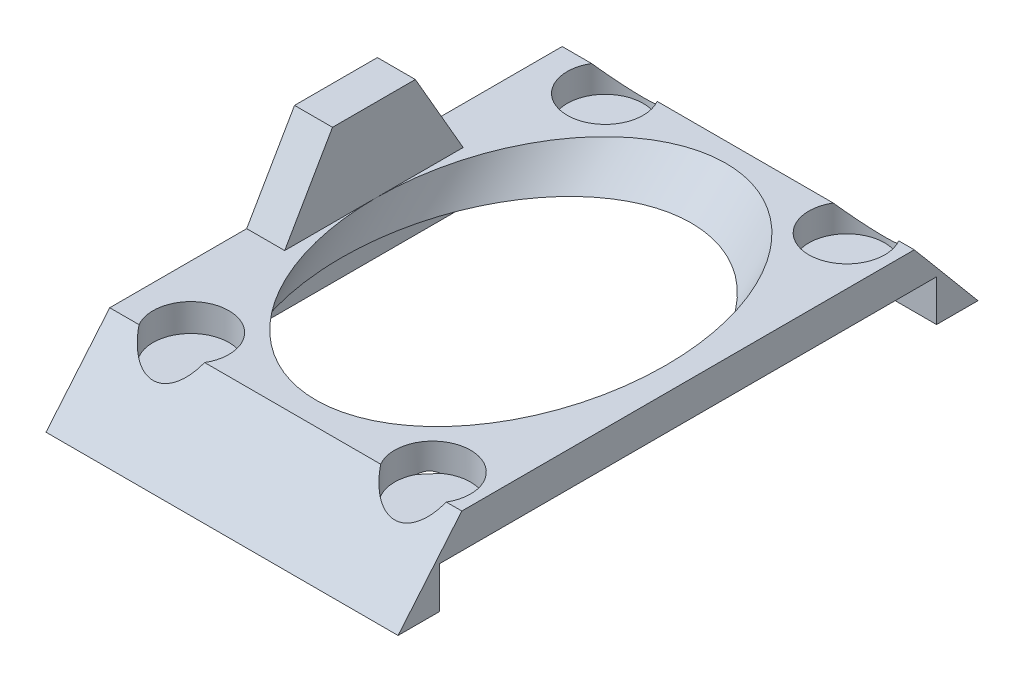
SolidWorks part; units mm, degrees
ref_plane "Front Plane" through (0, 0, 0) normal (0, 0, 1) x (1, 0, 0)
ref_plane "Top Plane" through (0, 0, 0) normal (0, 1, 0) x (1, 0, 0)
ref_plane "Right Plane" through (0, 0, 0) normal (1, 0, 0) x (0, 0, -1)
sketch "Sketch1" plane through (0, 0, 0) normal (0, 1, 0) x (1, 0, 0)
  line L1 (-13, 21) -> (12.5, 21)
  line L2 (-13, 21) -> (-13, -21)
  line L3 (-13, -21) -> (12.5, -21)
  line L4 (12.5, 21) -> (12.5, -21)
  dimension "D1" = 25.5
  dimension "D2" = 42
  dimension "D3" = 21
  dimension "D4" = 12.5
extrude "Boss-Extrude1" add sketch "Sketch1" along normal blind 5.5 contours L1 L4 L3 L2
ref_plane "Plane4" through (-13, 0, 0) normal (-1, 0, 0) x (0, 0, 1)
sketch "Sketch2" plane through (0, 0, 0) normal (0, -1, 0) x (1, 0, 0)
  line L1 (-12, 18) -> (13, 18)
  line L2 (-12, 18) -> (-12, -18)
  line L3 (-12, -18) -> (13, -18)
  line L4 (13, 18) -> (13, -18)
  line L5 (-13, -21) -> (-13, 21) construction
  dimension "D1" = 25
  dimension "D2" = 36
  dimension "D3" = 18
  dimension "D4" = 1
extrude "Cut-Extrude1" cut sketch "Sketch2" against normal blind 3
ref_plane "Plane1" through (0, 13.25, -13.25) normal (0, 0.7071, -0.7071) x (1, 0, 0)
sketch "Sketch3" plane through (0, 13.25, -13.25) normal (0, 0.7071, -0.7071) x (1, 0, 0)
  line L5 (-13, 10.9602) -> (12.5, 10.9602) construction
  line L6 (12.5, 10.9602) -> (12.5, -18.7383) construction
  circle A0 centre (0.25, -3.7898) radius 10.5
  dimension "D1" = 21
  dimension "D2" = 14.75
  dimension "D3" = 12.25
extrude "Cut-Extrude6" cut sketch "Sketch3" against normal blind 29
sketch "Sketch6" plane through (0, 5.5, 0) normal (0, 1, 0) x (1, 0, 0)
  line L0 (-39.5055, 0) -> (36.7045, 0) construction
  circle A0 centre (-8.5, 15) radius 2.75
  circle A1 centre (9, 15) radius 2.75
  circle A2 centre (-8.5, -15) radius 2.75
  circle A3 centre (9, -15) radius 2.75
  dimension "D1" = 5.5
  dimension "D4" = 5.5
  dimension "D2" = 15
  dimension "D3" = 8.5
  dimension "D5" = 9
  dimension "D6" = 15
extrude "Cut-Extrude7" cut sketch "Sketch6" against normal blind 2
sketch "Sketch7" plane through (0, 0, 0) normal (1, 0, 0) x (0, 0, -1)
  line L0 (-21, 0) -> (-12.8238, 9.744)
  line L1 (-12.8238, 9.744) -> (-21, 9.744)
  line L2 (-21, 9.744) -> (-21, 0)
  dimension "D1" = 90
  dimension "D2" = 40
extrude "Cut-Extrude8" cut sketch "Sketch7" against normal through all both and the other way through all
sketch "Sketch8" plane through (-13, 0, 0) normal (1, 0, 0) x (0, 0, -1)
  line L3 (-3, 11.5) -> (3, 11.5)
  line L5 (21, 5.5) -> (21, 0) construction
  line L6 (-6.4641, 5.5) -> (-3, 11.5)
  line L7 (21, 5.5) -> (-16.385, 5.5) construction
  line L8 (3, 11.5) -> (6.4641, 5.5)
  line L9 (6.4641, 5.5) -> (-6.4641, 5.5)
  dimension "D1" = 6
  dimension "D2" = 120
  dimension "D3" = 18
  dimension "D4" = 120
  dimension "D5" = 6
extrude "Boss-Extrude2" add sketch "Sketch8" along normal blind 2.75
sketch "Sketch9" plane through (-13, 0, 0) normal (1, 0, 0) x (0, 0, -1)
  line L0 (3, 11.5) -> (-3, 11.5) construction
  line L2 (21, 5.5) -> (21, 0) construction
  circle A0 centre (0, 8.5) radius 2.5
  dimension "D1" = 5
  dimension "D2" = 3
  dimension "D3" = 21
extrude "Cut-Extrude11" cut sketch "Sketch9" along normal blind 2.25 contours A0
sketch "Sketch10" plane through (0, 0, 0) normal (1, 0, 0) x (0, 0, -1)
  line L0 (21, 0) -> (15.9654, 6)
  line L1 (15.9654, 6) -> (21, 6)
  line L2 (21, 6) -> (21, 0)
  dimension "D1" = 40
  dimension "D2" = 6
extrude "Cut-Extrude12" cut sketch "Sketch10" against normal through all both and the other way through all
